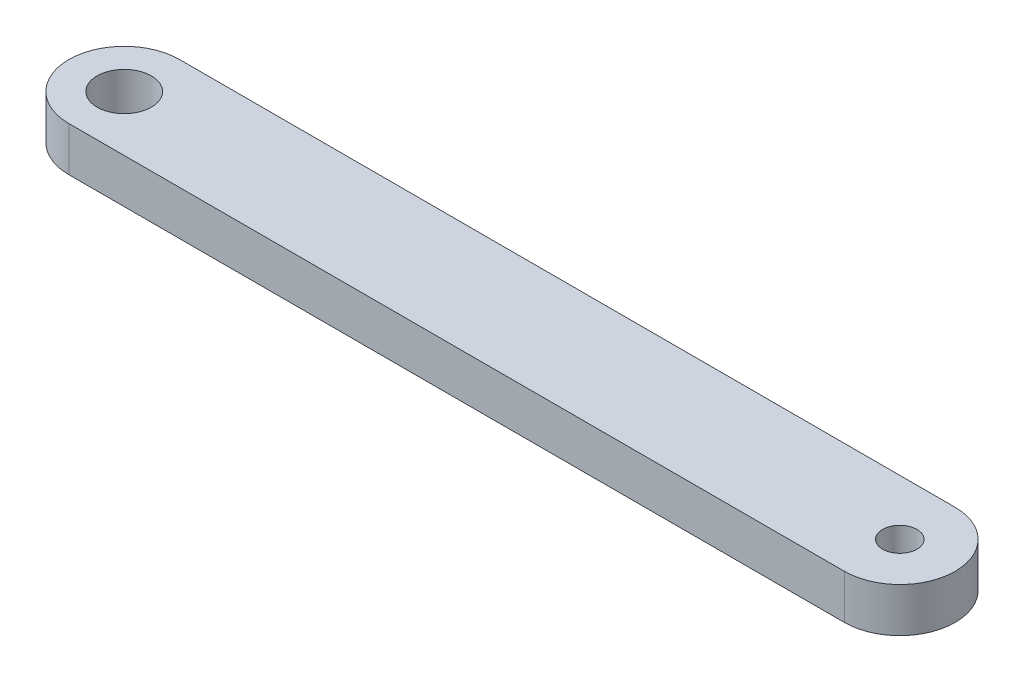
SolidWorks part; units mm, degrees
ref_plane "Front Plane" through (0, 0, 0) normal (0, 0, 1) x (1, 0, 0)
ref_plane "Top Plane" through (0, 0, 0) normal (0, 1, 0) x (1, 0, 0)
ref_plane "Right Plane" through (0, 0, 0) normal (1, 0, 0) x (0, 0, -1)
sketch "Sketch1" plane through (0, 0, 0) normal (0, 1, 0) x (1, 0, 0)
  line L0 (0, 0) -> (-70, 0) construction
  line L1 (0, -5) -> (-70, -5)
  line L2 (0, 5) -> (-70, 5)
  arc A0 (0, -5) -> (0, 5) centre (0, 0) ccw
  arc A1 (-70, 5) -> (-70, -5) centre (-70, 0) ccw
  circle A2 centre (-70, 0) radius 2.45
  circle A3 centre (0, 0) radius 1.55
  point P3 (-35, 0)
  dimension "D2" = 4.9
  dimension "D3" = 3.1
  dimension "D1" = 70
  dimension "D4" = 10
extrude "Boss-Extrude1" add sketch "Sketch1" along normal blind 4
